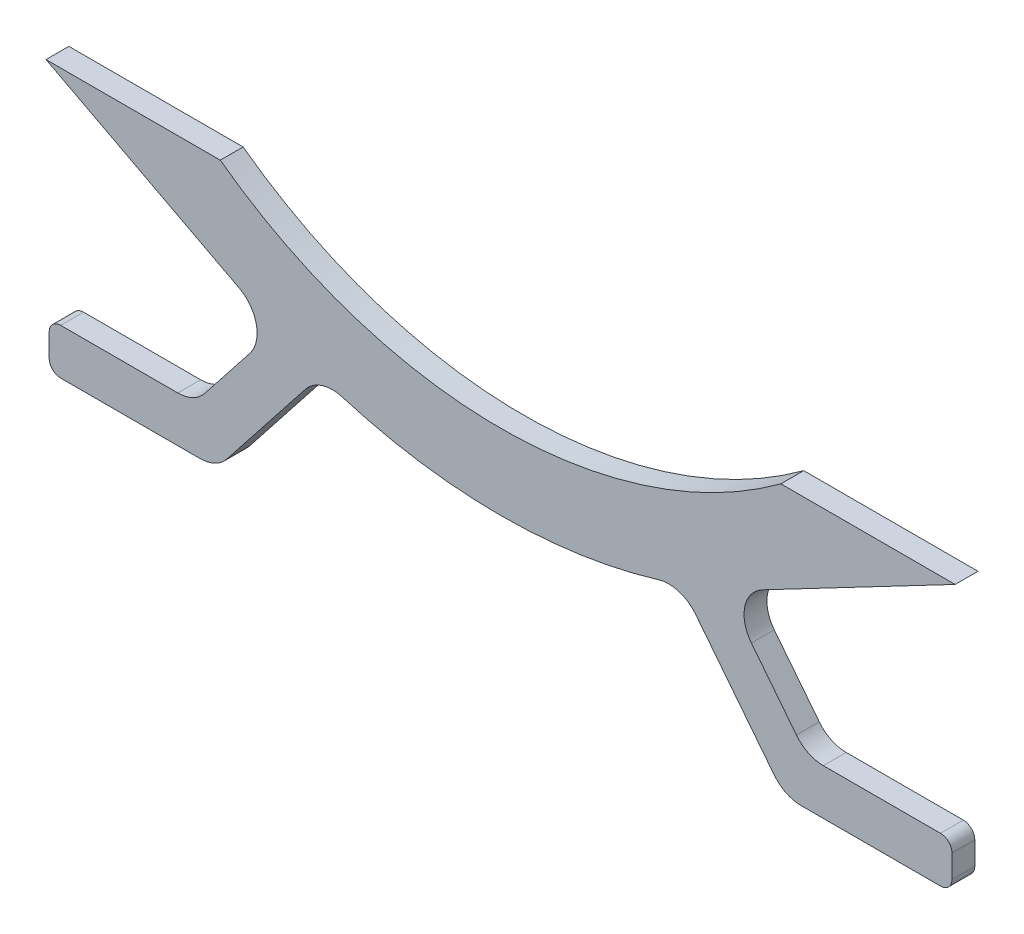
SolidWorks part; units mm, degrees
ref_plane "Front" through (0, 0, 0) normal (0, 0, 1) x (1, 0, 0)
ref_plane "Top" through (0, 0, 0) normal (0, 1, 0) x (1, 0, 0)
ref_plane "Right" through (0, 0, 0) normal (1, 0, 0) x (0, 0, -1)
sketch "Sketch1" plane through (0, 0, 0) normal (0, 0, 1) x (1, 0, 0)
  line L0 (218.4717, -3.175) -> (186.7217, -3.175)
  line L1 (199.4217, -3.175) -> (244.6655, -3.175) construction
  line L2 (-0.7938, -3.175) -> (30.9563, -3.175)
  line L3 (18.2563, -3.175) -> (-36.5125, -3.175) construction
  line L4 (108.839, 102.6854) -> (108.839, -207.9625) construction
  line L5 (-22.9235, -207.9625) -> (231.0765, -207.9625) construction
  line L6 (18.2563, -3.175) -> (30.9563, -3.175) construction
  arc A0 (218.4717, -3.175) -> (-0.7938, -3.175) centre (108.839, 102.6854) cw
  arc A1 (186.7217, -3.175) -> (30.9563, -3.175) centre (108.839, 102.6854) cw
  dimension "D5" = 152.4
  dimension "D1" = 12.7
  dimension "D2" = 31.75
  dimension "D3" = 12.7
extrude "Extrude1" add sketch "Sketch1" along normal mid plane 6.35
sketch "Sketch2" plane through (0, 0, -3.175) normal (0, 0, -1) x (-1, 0, 0)
  line L0 (16.5735, -77.7875) -> (-29.946, -77.7875)
  line L1 (-29.946, -77.7875) -> (-58.7274, -41.2402)
  line L2 (16.5735, -77.7875) -> (16.5735, -65.0875)
  line L3 (16.5735, -65.0875) -> (-23.7821, -65.0875)
  line L4 (-23.7821, -65.0875) -> (-46.4175, -36.3445)
  line L5 (22.9235, -207.9625) -> (22.9235, -80.9625) construction
  line L6 (22.9235, -80.9625) -> (-231.0765, -80.9625) construction
  line L7 (32.4485, 25.4) -> (32.4485, 41.275) construction
  line L10 (-186.7217, -3.175) -> (-218.4717, -3.175)
  line L11 (0.7937, -3.175) -> (-30.9563, -3.175)
  arc A1 (-218.4717, -3.175) -> (0.7937, -3.175) centre (-108.839, 102.6854) ccw construction
  arc A4 (-186.7217, -3.175) -> (-30.9563, -3.175) centre (-108.839, 102.6854) ccw
  arc A5 (-218.4717, -3.175) -> (0.7937, -3.175) centre (-108.839, 102.6854) ccw
  arc A7 (-58.7274, -41.2402) -> (-46.4175, -36.3445) centre (-108.839, 102.6854) ccw
  point P15 (32.4485, 33.3375)
  dimension "D1" = 12.7
  dimension "D2" = 3.175
  dimension "D3" = 12.7
  dimension "D5" = 6.35
  dimension "D4" = 0
extrude "Extrude2" add sketch "Sketch2" against normal up to surface (6.35 mm away) up to face at (108.839, -21.2007, 3.175)
sketch "Sketch3" plane through (0, 0, 3.175) normal (0, 0, 1) x (1, 0, 0)
  line L0 (179.5983, -32.2919) -> (235.1405, -3.175)
  line L1 (199.4217, -3.175) -> (244.6655, -3.175) construction
  line L2 (235.1405, -3.175) -> (218.4717, -3.175)
  line L10 (30.9563, -3.175) -> (-0.7938, -3.175)
  line L11 (46.4175, -36.3445) -> (23.7821, -65.0875)
  line L12 (23.7821, -65.0875) -> (-16.5735, -65.0875)
  line L13 (-16.5735, -65.0875) -> (-16.5735, -77.7875)
  line L14 (-16.5735, -77.7875) -> (29.946, -77.7875)
  line L15 (29.946, -77.7875) -> (58.7274, -41.2402)
  line L16 (218.4717, -3.175) -> (186.7217, -3.175)
  arc A0 (58.7274, -41.2402) -> (218.4717, -3.175) centre (108.839, 102.6854) ccw construction
  arc A4 (30.9563, -3.175) -> (186.7217, -3.175) centre (108.839, 102.6854) ccw
  arc A5 (-0.7938, -3.175) -> (46.4175, -36.3445) centre (108.839, 102.6854) ccw
  arc A6 (58.7274, -41.2402) -> (218.4717, -3.175) centre (108.839, 102.6854) ccw
  arc A9 (179.5983, -32.2919) -> (218.4717, -3.175) centre (108.839, 102.6854) ccw
  dimension "D2" = 9.525
  dimension "D3" = 0
extrude "Extrude3" add sketch "Sketch3" against normal up to surface (6.35 mm away) up to face at (56.5063, -42.7209, -3.175)
fillet "Fillet1" radius 9.525 4 edges at (46.4175, -36.3445, 0) (23.7821, -65.0875, 0) (58.7274, -41.2402, 0) (29.946, -77.7875, 0)
fillet "Fillet2" radius 3.175 2 edges at (-16.5735, -65.0875, 0) (-16.5735, -77.7875, 0)
ref_plane "Plane1" through (108.839, 0, 0) normal (1, 0, 0) x (0, 0, -1)
mirror "Mirror1" about plane through (108.839, 0, 0) normal (1, 0, 0) of "Extrude3", "Extrude2", "Fillet1", "Fillet2"
